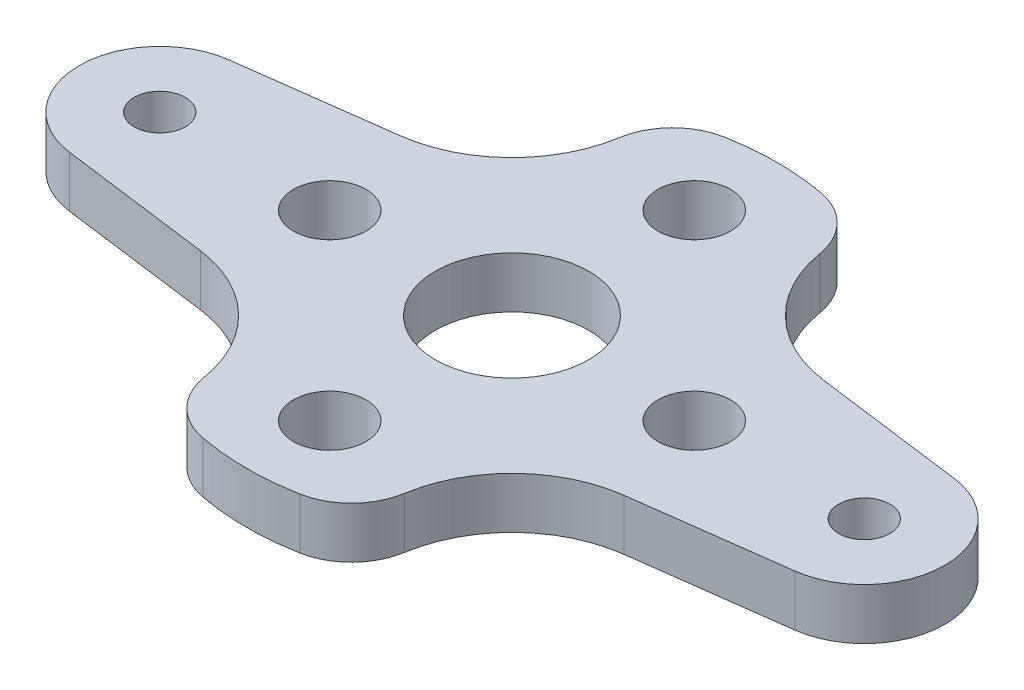
SolidWorks part; units mm, degrees
material "7075-T6, Plate (SS)"
ref_plane "Front Plane" through (0, 0, 0) normal (0, 0, 1) x (1, 0, 0)
ref_plane "Top Plane" through (0, 0, 0) normal (0, 1, 0) x (1, 0, 0)
ref_plane "Right Plane" through (0, 0, 0) normal (1, 0, 0) x (0, 0, -1)
sketch "Sketch1" plane through (0, 0, 0) normal (0, 1, 0) x (1, 0, 0)
  line L0 (0, 0) -> (0, 21.8652) construction
  line L1 (0, 0) -> (14.1869, 14.1869) construction
  line L2 (4.9572, 22.5178) -> (6.1926, 13.1344)
  line L3 (22.5178, -4.9572) -> (13.1344, -6.1926)
  line L4 (22.5178, 4.9572) -> (13.1344, 6.1926)
  line L5 (0, 0) -> (-14.1869, 14.1869) construction
  line L8 (-4.9572, 22.5178) -> (-6.1926, 13.1344)
  line L9 (-8.4853, 8.4853) -> (8.4853, -8.4853)
  arc A0 (-4.9572, 22.5178) -> (4.9572, 22.5178) centre (0, 21.8652) cw
  arc A1 (6.1926, 13.1344) -> (13.1344, 6.1926) centre (14.1869, 14.1869) ccw
  arc A2 (-6.1926, 13.1344) -> (-8.4853, 8.4853) centre (-14.1869, 14.1869) cw
  arc A3 (13.1344, -6.1926) -> (8.4853, -8.4853) centre (14.1869, -14.1869) ccw
  arc A4 (22.5178, -4.9572) -> (22.5178, 4.9572) centre (21.8652, 0) ccw
  point P18 (8.4853, 8.4853)
  dimension "D5" = 5
  dimension "D1" = 21.8652
  dimension "D2" = 45
  dimension "D3" = 12
  dimension "D4" = 7.5
extrude "Boss-Extrude1" add sketch "Sketch1" along normal blind 3.175
mirror "Mirror7" about plane through (-8.4853, 3.175, -8.4853) normal (0.7071, 0, -0.7071) of "Boss-Extrude1"
hole_wizard "1/8 (0.1250) Dowel Hole1" positions "Sketch2" profile "Sketch3" hole size "1/8" standard "ANSI Inch" end condition through all
sketch "Sketch2" plane through (0, 3.175, 0) normal (0, 1, 0) x (1, 0, 0)
  point P0 (0, 21.8652)
  point P3 (0, -21.8652)
  point P6 (-21.8652, 0)
  point P9 (21.8652, 0)
sketch "Sketch3" plane through (0, 3.175, -21.8652) normal (1, 0, 0) x (0, 0, 1)
  line L0 (0, 0) -> (0, 3.175)
  line L1 (0, 3.175) -> (1.5875, 3.175)
  line L2 (1.5875, 3.175) -> (1.5875, 0)
  line L5 (1.5875, 0) -> (0, 0)
  line L11 (0, -6.35) -> (0, 107.95) construction
  dimension "Thru Hole Dia." = 3.175
  dimension "Thru Hole Depth" = 3.175
sketch "Sketch4" plane through (0, 3.175, 0) normal (0, 1, 0) x (1, 0, 0)
  circle A0 centre (0, 0) radius 4.7625
  dimension "D1" = 9.525
extrude "Cut-Extrude1" cut sketch "Sketch4" against normal through all
hole_wizard "M4 Clearance Hole1" positions "Sketch5" profile "Sketch6" hole size "M4" standard "ANSI Metric" end condition through all
sketch "Sketch5" plane through (0, 3.175, 0) normal (0, 1, 0) x (1, 0, 0)
  line L0 (0, 0) -> (0, 11.3137) construction
  line L2 (0, 0) -> (11.3137, 0) construction
  circle A0 centre (0, 0) radius 11.3137 construction
  point P7 (0, 11.3137)
  point P12 (11.3137, 0)
  point P19 (0, -11.3137)
  point P21 (-11.3137, 0)
  dimension "D1" = 16
sketch "Sketch6" plane through (-11.3137, 3.175, 0) normal (1, 0, 0) x (0, 0, 1)
  line L0 (0, 0) -> (0, 3.175)
  line L1 (0, 3.175) -> (2.25, 3.175)
  line L2 (2.25, 3.175) -> (2.25, 0)
  line L5 (2.25, 0) -> (0, 0)
  line L11 (0, -6.35) -> (0, 107.95) construction
  dimension "Thru Hole Dia." = 4.5
  dimension "Thru Hole Depth" = 3.175
sketch "Sketch7" plane through (0, 3.175, 0) normal (0, 1, 0) x (1, 0, 0)
  line L8 (-4.9572, 22.5178) -> (-6.1926, 13.1344)
  line L9 (-13.1344, 6.1926) -> (-22.5178, 4.9572)
  line L10 (-22.5178, -4.9572) -> (-13.1344, -6.1926)
  line L11 (-6.1926, -13.1344) -> (-4.9572, -22.5178)
  line L12 (4.9572, -22.5178) -> (6.1926, -13.1344)
  line L13 (13.1344, -6.1926) -> (22.5178, -4.9572)
  line L14 (22.5178, 4.9572) -> (13.1344, 6.1926)
  line L15 (6.1926, 13.1344) -> (4.9572, 22.5178)
  line L16 (-5.8989, 15.3652) -> (-6.1926, 13.1344)
  line L17 (-13.1344, 6.1926) -> (-22.5178, 4.9572)
  line L18 (-22.5178, -4.9572) -> (-13.1344, -6.1926)
  line L19 (-6.1926, -13.1344) -> (-5.8989, -15.3652)
  line L20 (5.8989, -15.3652) -> (6.1926, -13.1344)
  line L21 (13.1344, -6.1926) -> (22.5178, -4.9572)
  line L22 (22.5178, 4.9572) -> (13.1344, 6.1926)
  line L23 (6.1926, 13.1344) -> (5.8989, 15.3652)
  arc A0 (5.8989, 15.3652) -> (-5.8989, 15.3652) centre (0, 0) ccw
  arc A1 (-5.8989, -15.3652) -> (5.8989, -15.3652) centre (0, 0) ccw
  arc A9 (4.9572, 22.5178) -> (-4.9572, 22.5178) centre (0, 21.8652) ccw
  arc A10 (-13.1344, 6.1926) -> (-6.1926, 13.1344) centre (-14.1869, 14.1869) ccw
  arc A11 (-22.5178, 4.9572) -> (-22.5178, -4.9572) centre (-21.8652, 0) ccw
  arc A12 (-6.1926, -13.1344) -> (-13.1344, -6.1926) centre (-14.1869, -14.1869) ccw
  arc A13 (-4.9572, -22.5178) -> (4.9572, -22.5178) centre (0, -21.8652) ccw
  arc A14 (13.1344, -6.1926) -> (6.1926, -13.1344) centre (14.1869, -14.1869) ccw
  arc A15 (22.5178, -4.9572) -> (22.5178, 4.9572) centre (21.8652, 0) ccw
  arc A16 (6.1926, 13.1344) -> (13.1344, 6.1926) centre (14.1869, 14.1869) ccw
  arc A18 (-13.1344, 6.1926) -> (-6.1926, 13.1344) centre (-14.1869, 14.1869) ccw
  arc A19 (-22.5178, 4.9572) -> (-22.5178, -4.9572) centre (-21.8652, 0) ccw
  arc A20 (-6.1926, -13.1344) -> (-13.1344, -6.1926) centre (-14.1869, -14.1869) ccw
  arc A22 (13.1344, -6.1926) -> (6.1926, -13.1344) centre (14.1869, -14.1869) ccw
  arc A23 (22.5178, -4.9572) -> (22.5178, 4.9572) centre (21.8652, 0) ccw
  arc A24 (6.1926, 13.1344) -> (13.1344, 6.1926) centre (14.1869, 14.1869) ccw
  point P1 (0, 0)
  circle M23 centre (0, 21.8652) radius 1.5875
  circle M24 centre (0, -21.8652) radius 1.5875
  arc M27 (4.9572, 22.5178) -> (-4.9572, 22.5178) centre (0, 21.8652) ccw
  line M28 (-4.9572, 22.5178) -> (-6.1926, 13.1344)
  line M34 (-6.1926, -13.1344) -> (-4.9572, -22.5178)
  arc M35 (-4.9572, -22.5178) -> (4.9572, -22.5178) centre (0, -21.8652) ccw
  line M36 (4.9572, -22.5178) -> (6.1926, -13.1344)
  line M42 (6.1926, 13.1344) -> (4.9572, 22.5178)
  dimension "D2" = 2.25
  dimension "D1" = 0
extrude "Cut-Extrude2" cut sketch "Sketch7" against normal through all contours A0 M42 M27 M28 M23 | A1 M34 M35 M36 M24
fillet "Fillet1" radius 4 4 edges at (5.8989, 1.5875, -15.3652) (-5.8989, 1.5875, -15.3652) (-5.8989, 1.5875, 15.3652) (5.8989, 1.5875, 15.3652)
equation "\"0.25iin\"=10"
